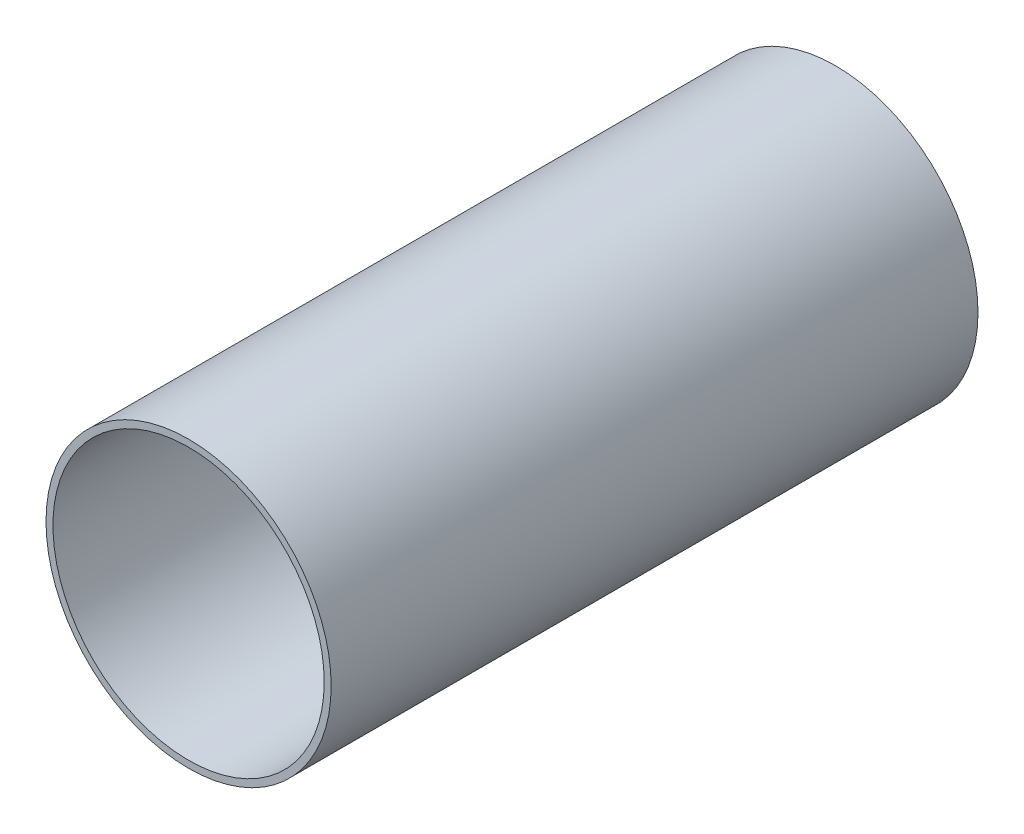
SolidWorks part; units mm, degrees
ref_plane "Plan de face" through (0, 0, 0) normal (0, 0, 1) x (1, 0, 0)
ref_plane "Plan de dessus" through (0, 0, 0) normal (0, 1, 0) x (1, 0, 0)
ref_plane "Plan de droite" through (0, 0, 0) normal (1, 0, 0) x (0, 0, -1)
sketch "Sketch1" plane through (0, 0, 0) normal (0, 0, 1) x (1, 0, 0)
  circle A0 centre (0, 0) radius 20.5
  dimension "D1" = 41
extrude "Boss-Extrude1" add sketch "Sketch1" along normal blind 93
sketch "Sketch2" plane through (0, 0, 93) normal (0, 0, 1) x (1, 0, 0)
  circle A0 centre (0, 0) radius 19.5
  dimension "D1" = 39
extrude "Cut-Extrude1" cut sketch "Sketch2" against normal through all
